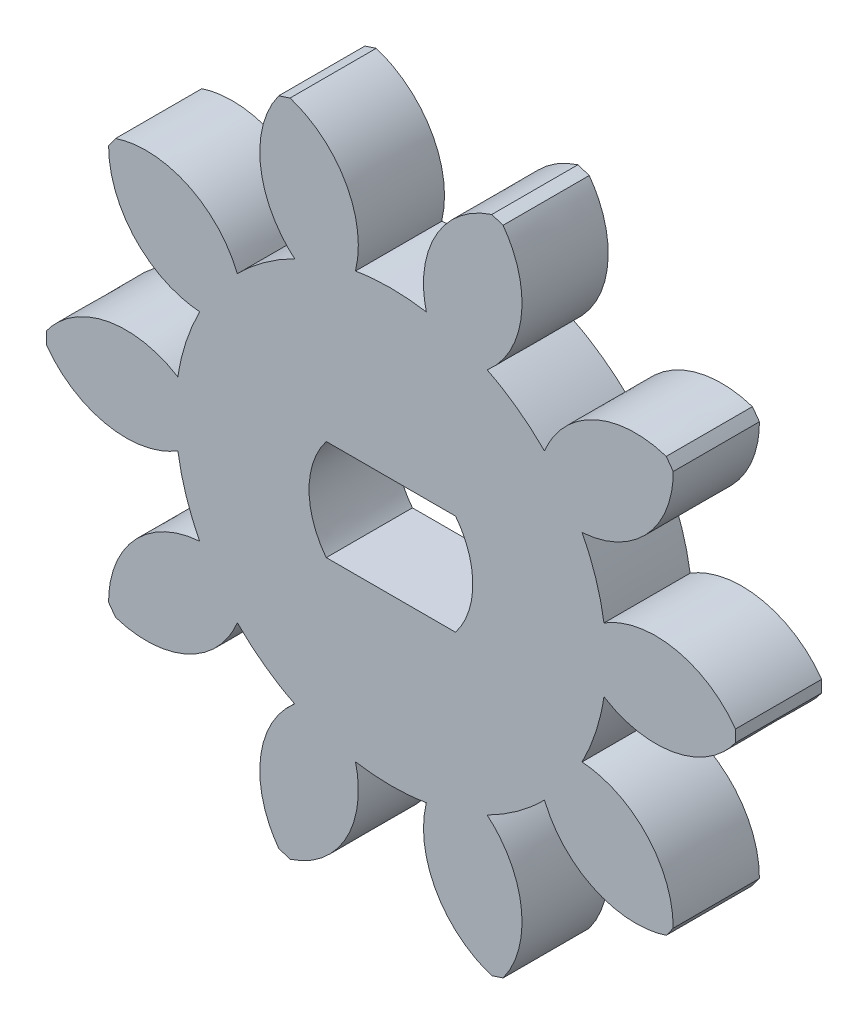
SolidWorks part; units mm, degrees
ref_plane "Alzado" through (0, 0, 0) normal (0, 0, 1) x (1, 0, 0)
ref_plane "Planta" through (0, 0, 0) normal (0, 1, 0) x (1, 0, 0)
ref_plane "Vista lateral" through (0, 0, 0) normal (1, 0, 0) x (0, 0, -1)
sketch "Croquis1" plane through (0, 0, 0) normal (0, 0, 1) x (1, 0, 0)
  line L72 (393.0323, -264.9744) -> (397.5323, -264.9744)
  line L73 (397.5323, -261.4744) -> (393.0323, -261.4744)
  spline S36 degree 3 poles (397.5323, -264.9744) (398.3328, -263.9451) (398.3328, -262.5037) (397.5323, -261.4744) knots 0 0 0 0 1 1 1 1
  spline S37 degree 3 poles (393.0323, -261.4744) (392.2317, -262.5037) (392.2317, -263.9451) (393.0323, -264.9744) knots 0 0 0 0 1 1 1 1
  spline S38 degree 3 poles (389.9362, -257.9643) (389.2564, -256.2998) (387.4055, -255.4441) (385.6972, -256.0046) knots 0 0 0 0 1 1 1 1
  spline S39 degree 3 poles (385.6972, -256.0046) (385.6141, -256.1148) (385.533, -256.2265) (385.4538, -256.3395) knots 0 0 0 0 1 1 1 1
  spline S40 degree 3 poles (385.4538, -256.3395) (385.4488, -258.1374) (386.8345, -259.6333) (388.6275, -259.7654) knots 0 0 0 0 1 1 1 1
  spline S41 degree 3 poles (388.6275, -259.7654) (388.2458, -260.4999) (387.9882, -261.2926) (387.8654, -262.1112) knots 0 0 0 0 1 1 1 1
  spline S42 degree 3 poles (387.8654, -262.1112) (386.337, -261.1642) (384.3367, -261.5599) (383.284, -263.0174) knots 0 0 0 0 1 1 1 1
  spline S43 degree 3 poles (383.284, -263.0174) (383.2817, -263.1554) (383.2817, -263.2934) (383.284, -263.4314) knots 0 0 0 0 1 1 1 1
  spline S44 degree 3 poles (383.284, -263.4314) (384.3367, -264.8889) (386.337, -265.2846) (387.8654, -264.3376) knots 0 0 0 0 1 1 1 1
  spline S45 degree 3 poles (387.8654, -264.3376) (387.9882, -265.1562) (388.2458, -265.9489) (388.6275, -266.6834) knots 0 0 0 0 1 1 1 1
  spline S46 degree 3 poles (388.6275, -266.6834) (386.8345, -266.8155) (385.4488, -268.3114) (385.4538, -270.1093) knots 0 0 0 0 1 1 1 1
  spline S47 degree 3 poles (385.4538, -270.1093) (385.533, -270.2223) (385.6141, -270.334) (385.6972, -270.4442) knots 0 0 0 0 1 1 1 1
  spline S48 degree 3 poles (385.6972, -270.4442) (387.4055, -271.0047) (389.2564, -270.149) (389.9362, -268.4846) knots 0 0 0 0 1 1 1 1
  spline S49 degree 3 poles (389.9362, -268.4846) (390.5167, -269.0746) (391.191, -269.5645) (391.9316, -269.9343) knots 0 0 0 0 1 1 1 1
  spline S50 degree 3 poles (391.9316, -269.9343) (390.5587, -271.0952) (390.3169, -273.1199) (391.3777, -274.5714) knots 0 0 0 0 1 1 1 1
  spline S51 degree 3 poles (391.3777, -274.5714) (391.5082, -274.6163) (391.6395, -274.6589) (391.7714, -274.6993) knots 0 0 0 0 1 1 1 1
  spline S52 degree 3 poles (391.7714, -274.6993) (393.4829, -274.1486) (394.4774, -272.3684) (394.049, -270.6223) knots 0 0 0 0 1 1 1 1
  spline S53 degree 3 poles (394.049, -270.6223) (394.8656, -270.7584) (395.699, -270.7584) (396.5155, -270.6223) knots 0 0 0 0 1 1 1 1
  spline S54 degree 3 poles (396.5155, -270.6223) (396.0871, -272.3684) (397.0816, -274.1486) (398.7931, -274.6993) knots 0 0 0 0 1 1 1 1
  spline S55 degree 3 poles (398.7931, -274.6993) (398.925, -274.6589) (399.0563, -274.6163) (399.1868, -274.5714) knots 0 0 0 0 1 1 1 1
  spline S56 degree 3 poles (399.1868, -274.5714) (400.2477, -273.1199) (400.0058, -271.0952) (398.6329, -269.9343) knots 0 0 0 0 1 1 1 1
  spline S57 degree 3 poles (398.6329, -269.9343) (399.3735, -269.5645) (400.0478, -269.0746) (400.6284, -268.4846) knots 0 0 0 0 1 1 1 1
  spline S58 degree 3 poles (400.6284, -268.4846) (401.3081, -270.149) (403.159, -271.0047) (404.8674, -270.4442) knots 0 0 0 0 1 1 1 1
  spline S59 degree 3 poles (404.8674, -270.4442) (404.9504, -270.334) (405.0315, -270.2223) (405.1107, -270.1093) knots 0 0 0 0 1 1 1 1
  spline S60 degree 3 poles (405.1107, -270.1093) (405.1158, -268.3114) (403.73, -266.8155) (401.937, -266.6834) knots 0 0 0 0 1 1 1 1
  spline S61 degree 3 poles (401.937, -266.6834) (402.3188, -265.9489) (402.5763, -265.1562) (402.6992, -264.3376) knots 0 0 0 0 1 1 1 1
  spline S62 degree 3 poles (402.6992, -264.3376) (404.2275, -265.2846) (406.2278, -264.8889) (407.2805, -263.4314) knots 0 0 0 0 1 1 1 1
  spline S63 degree 3 poles (407.2805, -263.4314) (407.2829, -263.2934) (407.2829, -263.1554) (407.2805, -263.0174) knots 0 0 0 0 1 1 1 1
  spline S64 degree 3 poles (407.2805, -263.0174) (406.2278, -261.5599) (404.2275, -261.1642) (402.6992, -262.1112) knots 0 0 0 0 1 1 1 1
  spline S65 degree 3 poles (402.6992, -262.1112) (402.5763, -261.2926) (402.3188, -260.4999) (401.937, -259.7654) knots 0 0 0 0 1 1 1 1
  spline S66 degree 3 poles (401.937, -259.7654) (403.73, -259.6333) (405.1158, -258.1374) (405.1107, -256.3395) knots 0 0 0 0 1 1 1 1
  spline S67 degree 3 poles (405.1107, -256.3395) (405.0315, -256.2265) (404.9504, -256.1148) (404.8674, -256.0046) knots 0 0 0 0 1 1 1 1
  spline S68 degree 3 poles (404.8674, -256.0046) (403.159, -255.4441) (401.3081, -256.2998) (400.6284, -257.9643) knots 0 0 0 0 1 1 1 1
  spline S69 degree 3 poles (400.6284, -257.9643) (400.0478, -257.3742) (399.3735, -256.8843) (398.6329, -256.5145) knots 0 0 0 0 1 1 1 1
  spline S70 degree 3 poles (398.6329, -256.5145) (400.0058, -255.3536) (400.2477, -253.3289) (399.1868, -251.8774) knots 0 0 0 0 1 1 1 1
  spline S71 degree 3 poles (399.1868, -251.8774) (399.0563, -251.8325) (398.925, -251.7898) (398.7931, -251.7495) knots 0 0 0 0 1 1 1 1
  spline S72 degree 3 poles (398.7931, -251.7495) (397.0816, -252.3002) (396.0871, -254.0804) (396.5155, -255.8265) knots 0 0 0 0 1 1 1 1
  spline S73 degree 3 poles (396.5155, -255.8265) (395.699, -255.6904) (394.8656, -255.6904) (394.049, -255.8265) knots 0 0 0 0 1 1 1 1
  spline S74 degree 3 poles (394.049, -255.8265) (394.4774, -254.0804) (393.4829, -252.3002) (391.7714, -251.7495) knots 0 0 0 0 1 1 1 1
  spline S75 degree 3 poles (391.7714, -251.7495) (391.6395, -251.7898) (391.5082, -251.8325) (391.3777, -251.8774) knots 0 0 0 0 1 1 1 1
  spline S76 degree 3 poles (391.3777, -251.8774) (390.3169, -253.3289) (390.5587, -255.3536) (391.9316, -256.5145) knots 0 0 0 0 1 1 1 1
  spline S77 degree 3 poles (391.9316, -256.5145) (391.191, -256.8843) (390.5167, -257.3742) (389.9362, -257.9643) knots 0 0 0 0 1 1 1 1
extrude "Saliente-Extruir1" add sketch "Croquis1" along normal blind 3
